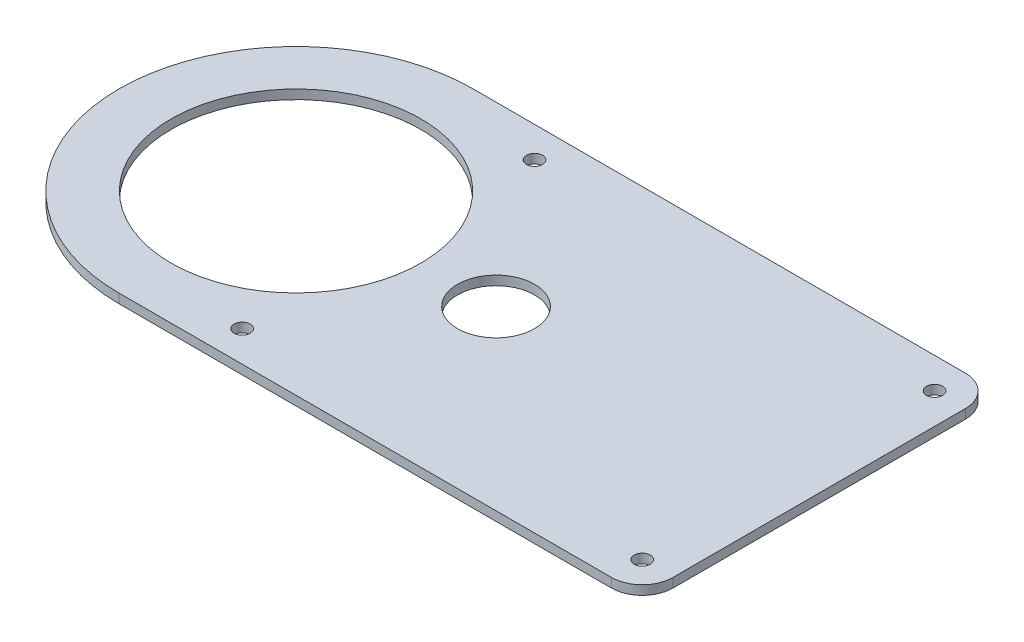
SolidWorks part; units mm, degrees
ref_plane "Front Plane" through (0, 0, 0) normal (0, 0, 1) x (1, 0, 0)
ref_plane "Top Plane" through (0, 0, 0) normal (0, 1, 0) x (1, 0, 0)
ref_plane "Right Plane" through (0, 0, 0) normal (1, 0, 0) x (0, 0, -1)
sketch "Sketch1" plane through (0, 0, 0) normal (0, 1, 0) x (1, 0, 0)
  line L0 (0, 57.5) -> (170, 57.5)
  line L1 (170, 57.5) -> (170, -57.5)
  line L2 (170, -57.5) -> (0, -57.5)
  circle A0 centre (0, 0) radius 57.5
  circle A1 centre (0, 0) radius 40.6
  dimension "D1" = 115
  dimension "D2" = 81.2
  dimension "D3" = 170
extrude "Boss-Extrude1" add sketch "Sketch1" along normal blind 3 contours A0 L2 L1 L0 | A0 A1
fillet "Fillet1" radius 10 2 edges at (170, 1.5, -57.5) (170, 1.5, 57.5)
sketch "Sketch2" plane through (0, 3, 0) normal (0, 1, 0) x (1, 0, 0)
  line L0 (170, 0) -> (104.452, 0) construction
  line L1 (170, 47.5) -> (170, -47.5) construction
  line L2 (95, -57.5) -> (95, 57.5) construction
  circle A0 centre (160, 47.5) radius 2.6
  circle A1 centre (160, -47.5) radius 2.6
  circle A2 centre (30, -47.5) radius 2.6
  circle A3 centre (30, 47.5) radius 2.6
  circle A4 centre (65, 0) radius 12.5
  dimension "D1" = 5.2
  dimension "D3" = 25
  dimension "D4" = 65
  dimension "D2" = 75
extrude "Cut-Extrude1" cut sketch "Sketch2" against normal through all
